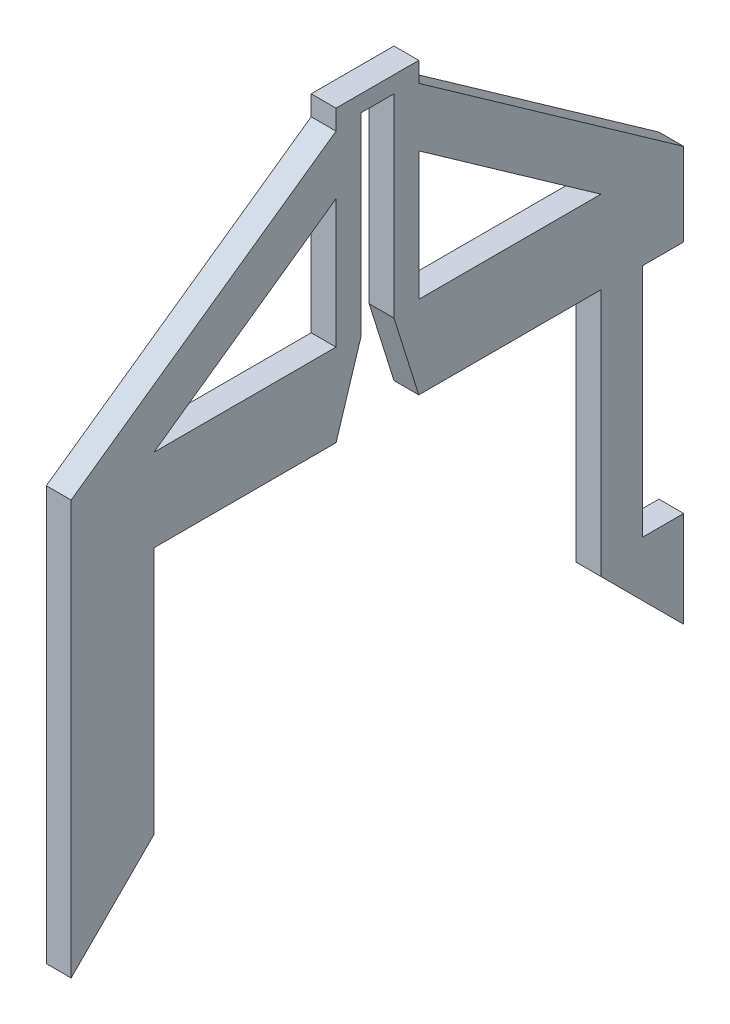
SolidWorks part; units mm, degrees
ref_plane "Front Plane" through (0, 0, 0) normal (0, 0, 1) x (1, 0, 0)
ref_plane "Top Plane" through (0, 0, 0) normal (0, 1, 0) x (1, 0, 0)
ref_plane "Right Plane" through (0, 0, 0) normal (1, 0, 0) x (0, 0, -1)
sketch "Sketch2" plane through (0, 0, 0) normal (1, 0, 0) x (0, 0, -1)
  line L1 (-27, 27) -> (27, 27)
  line L2 (-27, 27) -> (-27, -27)
  line L3 (-27, -27) -> (27, -27)
  line L4 (27, 27) -> (27, -27)
  line L5 (-27, 27) -> (27, -27) construction
  line L6 (-27, -27) -> (27, 27) construction
  line L7 (37, 37) -> (-37, 37)
  line L8 (37, 37) -> (37, -37)
  line L9 (37, -37) -> (-37, -37)
  line L10 (-37, 37) -> (-37, -37)
  line L11 (37, 37) -> (-37, -37) construction
  line L12 (37, -37) -> (-37, 37) construction
  point P0 (0, 0)
  point P5 (0, 0)
  dimension "D1" = 54
  dimension "D2" = 74
  dimension "D3" = 74
extrude "Boss-Extrude1" add sketch "Sketch2" along normal blind 3
sketch "Sketch3" plane through (3, 0, 0) normal (1, 0, 0) x (0, 0, -1)
  line L0 (37, 37) -> (-37, 37) construction
  line L1 (-5, 37) -> (5, 37)
  line L2 (-5, 37) -> (-5, 62)
  line L3 (-5, 62) -> (5, 62)
  line L4 (5, 37) -> (5, 62)
  line L5 (-37, 37) -> (-37, -37) construction
  dimension "D1" = 10
  dimension "D2" = 25
  dimension "D3" = 32
extrude "Boss-Extrude2" add sketch "Sketch3" against normal up to surface (3 mm away) up to face at (0, 0, 0)
sketch "Sketch4" plane through (0, 0, 0) normal (-1, 0, 0) x (0, 0, 1)
  line L0 (-5, 62) -> (5, 62) construction
  line L1 (5, 62) -> (5, 37) construction
  circle A0 centre (0, 57) radius 5
  line M4 (5, 37) -> (5, 62)
  line M5 (5, 62) -> (-5, 62)
  line M6 (-5, 62) -> (-5, 37)
  dimension "D1" = 5
  dimension "D2" = 5
  dimension "D3" = 5
extrude "Cut-Extrude1" cut sketch "Sketch4" against normal up to surface (3 mm away) contours A0 M5 M6 | A0 M4 M5 up to face at (3, 24.75, -4)
sketch "Sketch6" plane through (3, 0, 0) normal (1, 0, 0) x (0, 0, -1)
  line L0 (-37, 37) -> (1.5515, 64.217)
  line L1 (-37, 37) -> (-27, 37)
  line L2 (-5, 37) -> (-37, 37) construction
  line L3 (-27, 37) -> (-5, 52.5318)
  line L4 (-5, 57) -> (-5, 37) construction
  line L5 (37, 37) -> (-3.6773, 65.7189)
  line L6 (37, 37) -> (27, 37)
  line L7 (37, 37) -> (5, 37) construction
  line L8 (27, 37) -> (5, 52.5318)
  line L9 (5, 37) -> (5, 57) construction
  line L10 (-5, 52.5318) -> (-5, 57)
  line L11 (5, 52.5318) -> (5, 57)
  arc A0 (5, 57) -> (-5, 57) centre (0, 57) ccw construction
  circle A1 centre (0, 57) radius 5
  arc M5 (5, 57) -> (-5, 57) centre (0, 57) ccw
  line M6 (-5, 57) -> (-5, 37)
  line M7 (-5, 37) -> (-37, 37)
  line M11 (37, 37) -> (5, 37)
  line M12 (5, 37) -> (5, 57)
  dimension "D8" = 10
  dimension "D1" = 5.001
  dimension "D2" = 47.1909
  dimension "D3" = 26.9302
  dimension "D4" = 49.7937
  dimension "D5" = 5.0017
  dimension "D6" = 26.9302
  dimension "D7" = 10
extrude "Boss-Extrude3" add sketch "Sketch6" against normal up to surface (3 mm away) contours L8 L5 L0 L3 M11 M7 M6 M5 M12 up to face at (0, 0, 0)
sketch "Sketch7" plane through (0, 0, 0) normal (-1, 0, 0) x (0, 0, 1)
  line L0 (37, 37) -> (-0.0007, 63.1222) construction
  line L1 (-37, 37) -> (-0.0007, 63.1222) construction
  line L2 (-0.0007, 63.1222) -> (-2.8844, 61.0862)
  line L3 (-0.0007, 63.1222) -> (2.8831, 61.0863)
  circle A0 centre (-0.0006, 57.0016) radius 5
  line M5 (37, 37) -> (-0.0007, 63.1222)
  line M6 (-0.0007, 63.1222) -> (-37, 37)
  dimension "D1" = 10
  dimension "D2" = 5
  dimension "D3" = 5
extrude "Cut-Extrude2" cut sketch "Sketch7" against normal up to surface (3 mm away) contours A0 M5 M6 up to face at (3, 44.7659, 8.6667)
sketch "Sketch8" plane through (3, 0, 0) normal (1, 0, 0) x (0, 0, -1)
  line L0 (37, 37) -> (2.8844, 61.0862) construction
  line L1 (-37, 37) -> (-2.8831, 61.0863) construction
  line L2 (-37, -18.4121) -> (-37, -37)
  line L3 (-37, 37) -> (-37, -37) construction
  line L4 (-37, -37) -> (37, -37)
  line L5 (37, -37) -> (37, -18.4127)
  line L7 (-27, -22.5423) -> (-27, -27)
  line L8 (-27, 27) -> (-27, -27) construction
  line L9 (-27, -27) -> (1.004, -26.994)
  line L10 (1.004, -26.994) -> (27, -27)
  line L11 (27, -27) -> (27, -22.5428)
  line L12 (27, -27) -> (27, 27) construction
  circle A0 centre (0.0006, 57.0016) radius 5
  circle A1 centre (0.0006, 57.0016) radius 84.0016
  line M1 (27, 27) -> (27, -27)
  line M2 (27, -27) -> (-27, -27)
  line M3 (-27, -27) -> (-27, 27)
  line M13 (-37, 37) -> (-37, -37)
  line M14 (-37, -37) -> (37, -37)
  line M15 (37, -37) -> (37, 37)
  dimension "D1" = 10
  dimension "D2" = 5
  dimension "D3" = 5
  dimension "D4" = 168.0033
  dimension "D5" = 18.5873
extrude "Cut-Extrude3" cut sketch "Sketch8" against normal up to surface (3 mm away) contours A1 M13 M14 M15 M1 M2 M3 up to face at (0, 0, 0)
sketch "Sketch9" plane through (0, 0, 0) normal (-1, 0, 0) x (0, 0, 1)
  line L0 (-2.0006, 54.0016) -> (-2.0006, 27)
  line L1 (-2.0006, 60.0016) -> (1.9994, 60.0016)
  line L2 (-2.0006, 60.0016) -> (-2.0006, 54.0016)
  line L3 (-2.0006, 54.0016) -> (1.9994, 54.0016)
  line L4 (1.9994, 60.0016) -> (1.9994, 54.0016)
  line L5 (-2.0006, 60.0016) -> (1.9994, 54.0016) construction
  line L6 (-2.0006, 54.0016) -> (1.9994, 60.0016) construction
  line L7 (-27, 27) -> (27, 27) construction
  line L8 (-2.0006, 27) -> (1.9994, 27)
  line L9 (1.9994, 27) -> (1.9994, 54.0016)
  line L10 (-2.0006, 27) -> (-5.0006, 27)
  line L11 (-5.0006, 27) -> (-2.0006, 36.5394)
  line L12 (1.9994, 36.5409) -> (4.9944, 27)
  line L13 (4.9944, 27) -> (1.9994, 27)
  circle A0 centre (-0.0006, 57.0016) radius 5
  dimension "D1" = 10
  dimension "D2" = 6
  dimension "D3" = 4
  dimension "D4" = 10
  dimension "D5" = 3
  dimension "D6" = 10
  dimension "D7" = 2.9951
extrude "Cut-Extrude4" cut sketch "Sketch9" against normal up to surface (3 mm away) contours L12 L9 | A0 L0 L9 | L11 L9 L0 | L0 A0 L9 L3 | L4 L1 L2 L3
sketch "Sketch10" plane through (0, 0, 0) normal (-1, 0, 0) x (0, 0, 1)
  line L0 (37, 37) -> (2.8831, 61.0863) construction
  line L1 (-37, 37) -> (-2.8844, 61.0862) construction
  line L2 (-5.0006, 52.0016) -> (-5.0006, 62.0016)
  line L3 (-5.0006, 52.0016) -> (4.9994, 52.0016)
  line L4 (-5.0006, 62.0016) -> (4.9994, 62.0016)
  line L5 (4.9994, 52.0016) -> (4.9994, 62.0016)
  line L6 (-5.0006, 52.0016) -> (4.9994, 62.0016) construction
  line L7 (-5.0006, 62.0016) -> (4.9994, 52.0016) construction
  circle A0 centre (-0.0006, 57.0016) radius 5
  line M7 (1.9994, 60.0016) -> (1.9994, 36.5409)
  line M13 (37, 37) -> (2.8831, 61.0863)
  arc M14 (2.8831, 61.0863) -> (-2.8844, 61.0862) centre (-0.0006, 57.0016) ccw
  line M15 (-2.8844, 61.0862) -> (-37, 37)
  line M21 (-2.0006, 36.5394) -> (-2.0006, 60.0016)
  line M22 (-2.0006, 60.0016) -> (1.9994, 60.0016)
  dimension "D1" = 10
  dimension "D2" = 5
  dimension "D3" = 5
  dimension "D4" = 10
  dimension "D5" = 10
extrude "Boss-Extrude4" add sketch "Sketch10" against normal up to surface (3 mm away) contours L4 L2 M15 M14 | A0 M14 M21 M22 M7 | L5 L4 M13 M14 up to face at (3, 39.5886, -16)
sketch "Sketch11" plane through (3, 0, 0) normal (1, 0, 0) x (0, 0, -1)
  line L0 (-27, 27) -> (-27, -3)
  line L1 (-27, 27) -> (-27, -22.5423) construction
  line L2 (-37, 37) -> (-37, -18.4121) construction
  line L3 (-27, -3) -> (-37, -13)
  line L4 (-27, -3) -> (-27, -13)
  line L5 (-37, -13) -> (-27, -13)
  line L6 (-37, -13) -> (-37, -22.5423)
  line L7 (-37, -22.5423) -> (-27, -22.5423)
  line L8 (-27, -13) -> (-27, -22.5423)
  line L9 (27, 27) -> (27, -3)
  line L10 (27, -22.5428) -> (27, 27) construction
  line L12 (37, -18.4127) -> (37, 37) construction
  line L13 (27, -13) -> (27, -3)
  line L14 (37, -13) -> (27, -13)
  line L15 (37, -13) -> (37, -22.5428)
  line L16 (37, -22.5428) -> (27, -22.5428)
  line L17 (27, -13) -> (27, -22.5428)
  line L18 (27, -3) -> (37, -13)
  circle A0 centre (-37, -3) radius 10
  circle A1 centre (37, -3) radius 10
  dimension "D1" = 20
  dimension "D2" = 40
  dimension "D3" = 20
  dimension "D4" = 40
extrude "Cut-Extrude6" cut sketch "Sketch11" against normal up to surface (3 mm away) contours L3 A0 | A0 L5 L15 | L5 L13 L14 L15 | L6 L14 L4 L5 | A1 L4 L14 | L18 A1
sketch "Sketch12" plane through (3, 0, 0) normal (1, 0, 0) x (0, 0, -1)
  line L0 (37, -13) -> (37, 37) construction
  line L1 (37, 27) -> (32, 27)
  line L2 (37, 27) -> (37, -1.4)
  line L3 (37, -1.4) -> (32, -1.4)
  line L4 (32, 27) -> (32, -1.4)
  line L5 (27, 27) -> (5.0006, 27) construction
  dimension "D1" = 28.4
  dimension "D2" = 5
  dimension "D3" = 0
extrude "Cut-Extrude7" cut sketch "Sketch12" against normal blind 3
